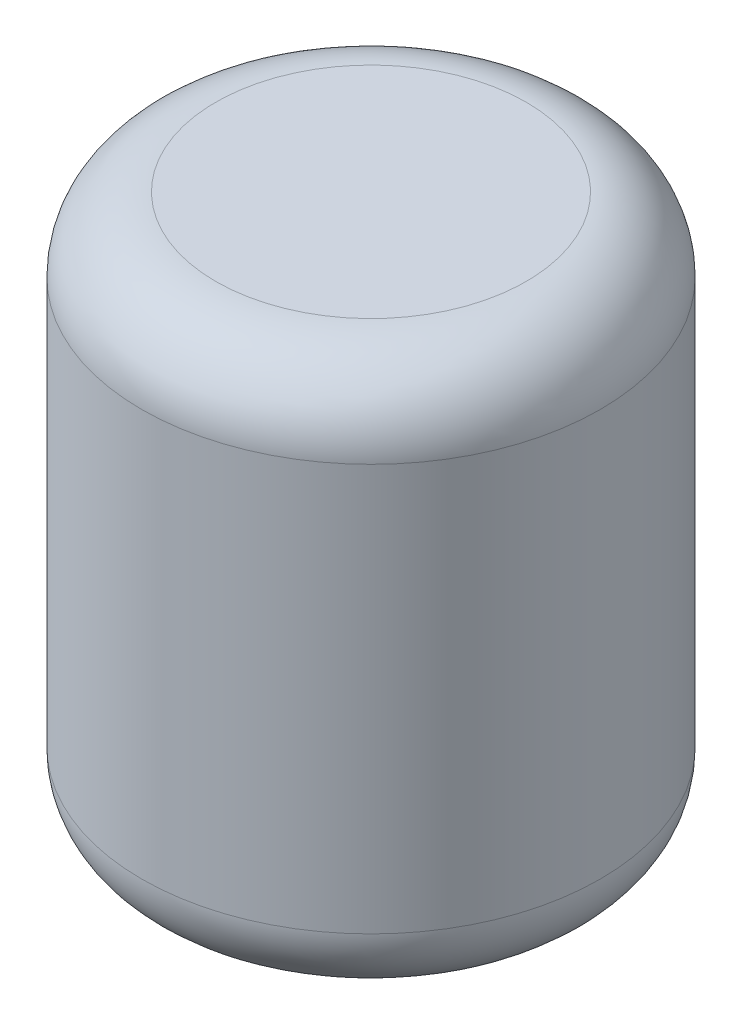
SolidWorks part; units mm, degrees
ref_plane "Ebene vorne" through (0, 0, 0) normal (0, 0, 1) x (1, 0, 0)
ref_plane "Ebene oben" through (0, 0, 0) normal (0, 1, 0) x (1, 0, 0)
ref_plane "Ebene rechts" through (0, 0, 0) normal (1, 0, 0) x (0, 0, -1)
sketch "Skizze1" plane through (0, 0, 0) normal (0, 1, 0) x (1, 0, 0)
  circle A0 centre (0, 0) radius 31
  dimension "D1" = 62
extrude "Aufsatz-Linear austragen1" add sketch "Skizze1" along normal mid plane 75
fillet "Verrundung1" radius 10 2 edges at (0, 37.5, 31) (0, -37.5, 31)
